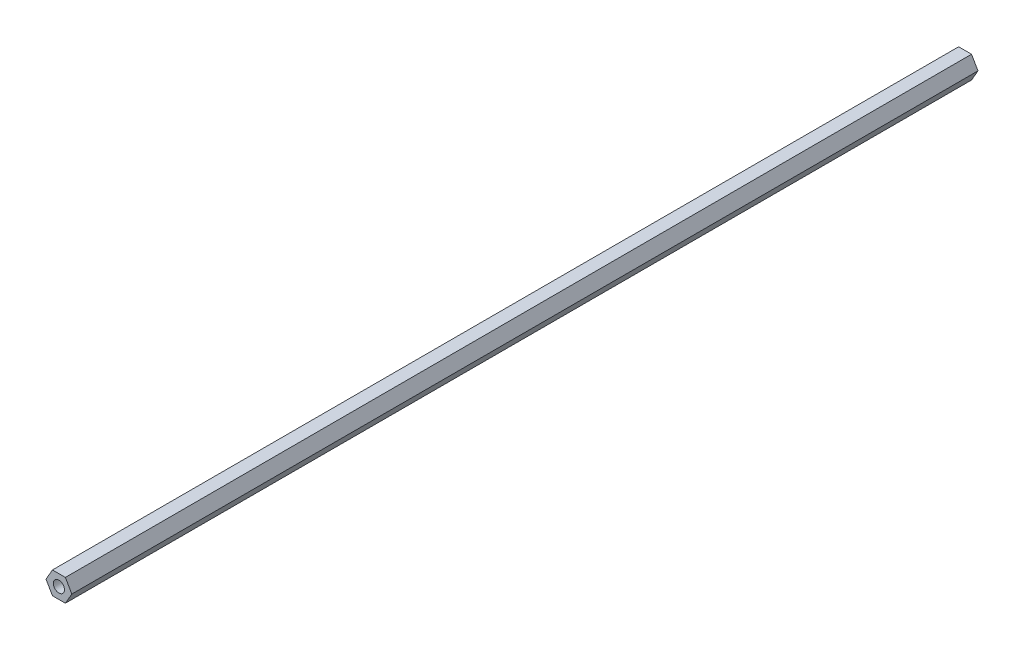
SolidWorks part; units mm, degrees
ref_plane "Front Plane" through (0, 0, 0) normal (0, 0, 1) x (1, 0, 0)
ref_plane "Top Plane" through (0, 0, 0) normal (0, 1, 0) x (1, 0, 0)
ref_plane "Right Plane" through (0, 0, 0) normal (1, 0, 0) x (0, 0, -1)
sketch "Sketch1" plane through (0, 0, 0) normal (0, 0, 1) x (1, 0, 0)
  line L0 (0, 6.35) -> (0, 0)
  line L1 (-7.3323, 0) -> (-3.6662, -6.35)
  line L2 (-3.6662, -6.35) -> (3.6662, -6.35)
  line L3 (3.6662, -6.35) -> (7.3323, 0)
  line L4 (7.3323, 0) -> (3.6662, 6.35)
  line L5 (3.6662, 6.35) -> (-3.6662, 6.35)
  line L6 (-3.6662, 6.35) -> (-7.3323, 0)
  circle A0 centre (0, 0) radius 6.35 construction
  dimension "D1" = 6.35
extrude "Boss-Extrude1" add sketch "Sketch1" along normal offset from surface (514.4834 mm away) 25.4
sketch "Sketch2" plane through (0, 0, 514.4834) normal (0, 0, 1) x (1, 0, 0)
  circle A0 centre (0, 0) radius 3.175
  dimension "D1" = 6.35
extrude "Cut-Extrude1" cut sketch "Sketch2" against normal through all both and the other way through all contours A0
sketch "Sketch3" plane through (0, 0, 0) normal (0, 0, -1) x (-1, 0, 0)
  line L1 (3.6662, -6.35) -> (7.3323, 0)
  line L2 (7.3323, 0) -> (3.6662, 6.35)
  line L3 (3.6662, 6.35) -> (-3.6662, 6.35)
  line L4 (-3.6662, 6.35) -> (-7.3323, 0)
  line L5 (-7.3323, 0) -> (-3.6662, -6.35)
  line L6 (-3.6662, -6.35) -> (3.6662, -6.35)
  circle A0 centre (0, 0) radius 6.35 construction
